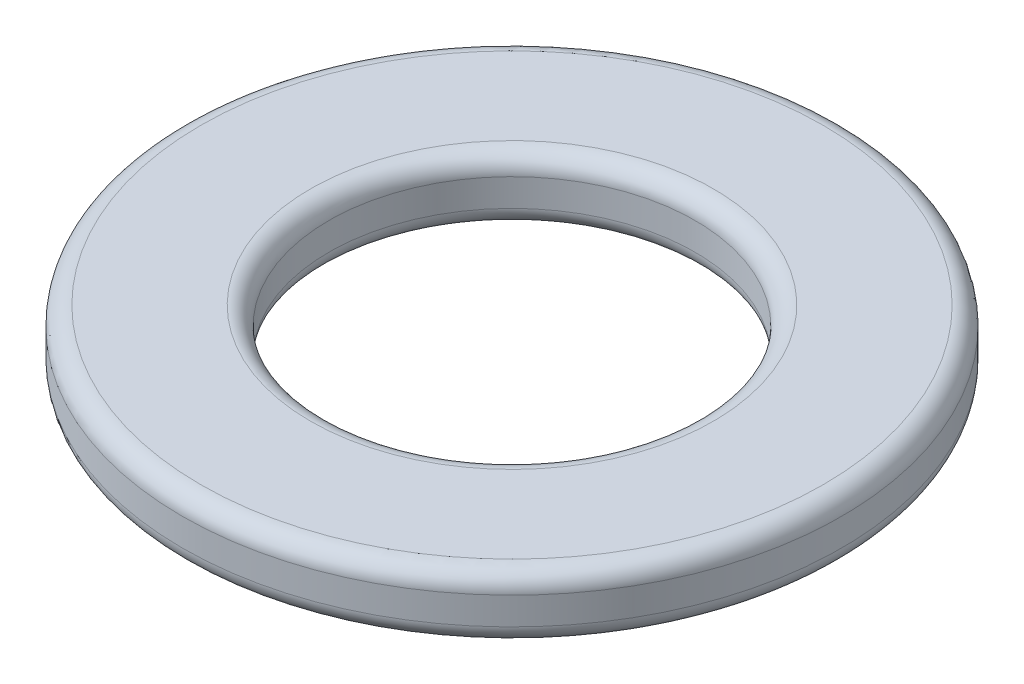
SolidWorks part; units mm, degrees
ref_plane "Front Plane" through (0, 0, 0) normal (0, 0, 1) x (1, 0, 0)
ref_plane "Top Plane" through (0, 0, 0) normal (0, 1, 0) x (1, 0, 0)
ref_plane "Right Plane" through (0, 0, 0) normal (1, 0, 0) x (0, 0, -1)
sketch "Sketch1" plane through (0, 0, 0) normal (0, 1, 0) x (1, 0, 0)
  circle A0 centre (0, 0) radius 9
  circle A1 centre (0, 0) radius 5
  dimension "D1" = 10
  dimension "D2" = 18
extrude "Boss-Extrude1" add sketch "Sketch1" along normal blind 1.75
fillet "Fillet1" radius 0.5 4 edges at (0, 1.75, 5) (0, 0, 9) (0, 0, 5) (0, 1.75, 9)
